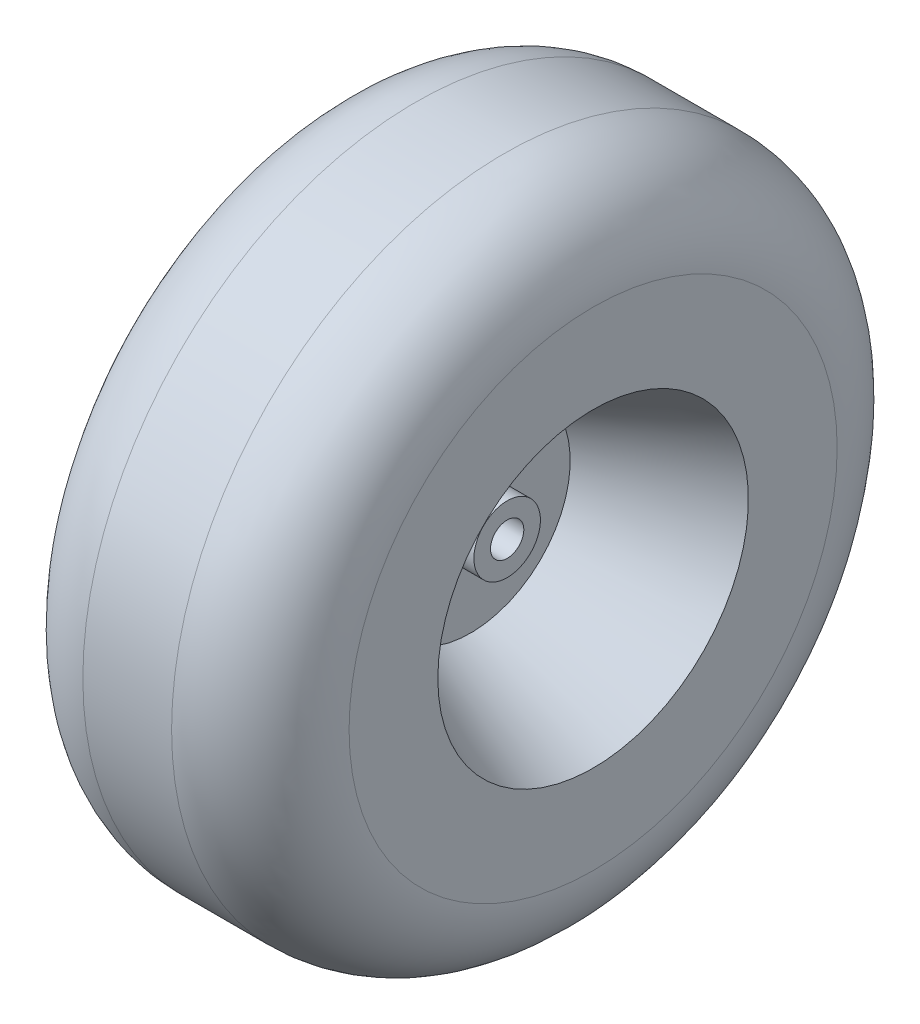
SolidWorks part; units mm, degrees
ref_plane "Front Plane" through (0, 0, 0) normal (0, 0, 1) x (1, 0, 0)
ref_plane "Top Plane" through (0, 0, 0) normal (0, 1, 0) x (1, 0, 0)
ref_plane "Right Plane" through (0, 0, 0) normal (1, 0, 0) x (0, 0, -1)
sketch "Sketch1" plane through (0, 0, 0) normal (0, 0, 1) x (1, 0, 0)
  line L0 (0, 0) -> (0, 190.5) construction
  line L1 (-76.2, 190.5) -> (76.2, 190.5) construction
  line L2 (76.2, 190.5) -> (76.2, 88.9) construction
  line L3 (-76.2, 0) -> (76.2, 0) construction
  line L4 (0, 0) -> (0, 9.525) construction
  line L5 (-26.9875, 9.525) -> (26.9875, 9.525)
  line L6 (76.2, 88.9) -> (76.2, 0) construction
  line L7 (26.9875, 9.525) -> (26.9875, 19.05)
  line L8 (26.9875, 19.05) -> (6.1126, 19.05)
  line L9 (6.1126, 19.05) -> (6.1126, 56.9746)
  line L10 (6.1126, 56.9746) -> (76.2, 88.9)
  line L11 (-25.4, 190.5) -> (25.4, 190.5)
  line L12 (76.2, 88.9) -> (76.2, 139.7)
  line L13 (-76.2, 88.9) -> (-76.2, 0) construction
  line L14 (-76.2, 190.5) -> (-76.2, 88.9) construction
  line L15 (-76.2, 88.9) -> (-76.2, 139.7)
  line L16 (-6.1126, 56.9746) -> (-76.2, 88.9)
  line L17 (-6.1126, 19.05) -> (-6.1126, 56.9746)
  line L18 (-26.9875, 19.05) -> (-6.1126, 19.05)
  line L19 (-26.9875, 9.525) -> (-26.9875, 19.05)
  line L20 (25.4, 190.5) -> (25.4, 139.7) construction
  line L21 (25.4, 139.7) -> (76.2, 139.7) construction
  arc A0 (25.4, 190.5) -> (76.2, 139.7) centre (25.4, 139.7) cw
  arc A1 (-25.4, 190.5) -> (-76.2, 139.7) centre (-25.4, 139.7) ccw
  point P11 (0, 9.525)
  dimension "D8" = 50.8
  dimension "D1" = 190.5
  dimension "D2" = 76.2
  dimension "D3" = 101.6
  dimension "D4" = 9.525
  dimension "D5" = 49.2125
  dimension "D6" = 9.525
revolve "Revolve1" add sketch "Sketch1" angle 360 about L3
sketch "Sketch2" plane through (0, 0, 0) normal (1, 0, 0) x (0, 0, -1)
  line L0 (0, 0) -> (0, -190.5) construction
  line L1 (0, 0) -> (0, 190.5)
  circle A0 centre (0, 0) radius 190.5
